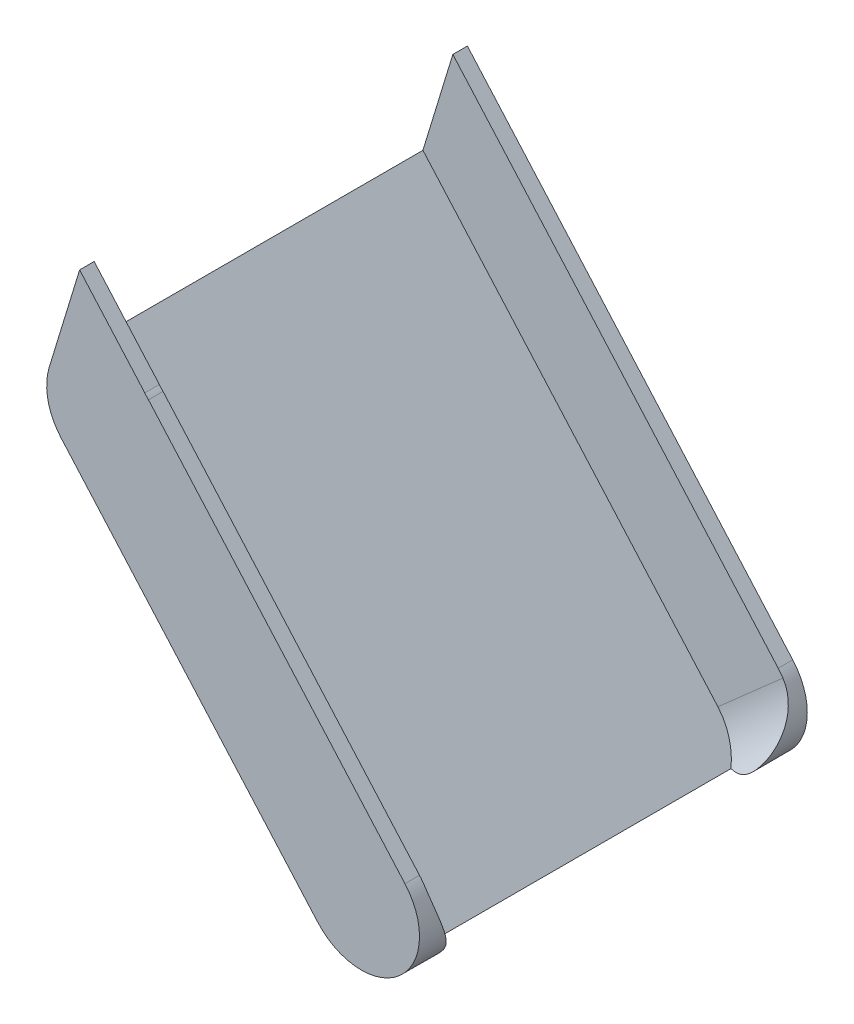
SolidWorks part; units mm, degrees
material "EPDM"
ref_plane "Front Plane" through (0, 0, 0) normal (0, 0, 1) x (1, 0, 0)
ref_plane "Top Plane" through (0, 0, 0) normal (0, 1, 0) x (1, 0, 0)
ref_plane "Right Plane" through (0, 0, 0) normal (1, 0, 0) x (0, 0, -1)
sketch "Sketch1" plane through (0, 0, 0) normal (0, 0, 1) x (1, 0, 0)
  line L0 (0, 0) -> (132.2876, -150) construction
  line L1 (22.5, 19.8431) -> (154.7876, -130.1569)
  line L2 (-22.5, -19.8431) -> (109.7876, -169.8431)
  arc A0 (22.5, 19.8431) -> (-22.5, -19.8431) centre (0, 0) ccw
  arc A1 (109.7876, -169.8431) -> (154.7876, -130.1569) centre (132.2876, -150) ccw
  point P3 (66.1438, -75)
  dimension "D1" = 30
  dimension "D2" = 150
  dimension "D3" = 200
extrude "Boss-Extrude4" add sketch "Sketch1" along normal blind 200
sketch "Sketch4" plane through (22.5, 19.8431, 0) normal (0.75, 0.6614, 0) x (0, 0, -1)
  line L2 (-192.5, 51.3214) -> (-192.5, -204.0082)
  line L4 (-7.5, 51.3214) -> (-7.5, -204.0082)
  line L6 (-200, -200) -> (-200, 0) construction
  line L7 (-192.5, 51.3214) -> (-7.5, 51.3214)
  line L8 (-157.5, -239.0082) -> (-42.5, -239.0082)
  arc A0 (-42.5, -239.0082) -> (-7.5, -204.0082) centre (-42.5, -204.0082) ccw
  arc A1 (-157.5, -239.0082) -> (-192.5, -204.0082) centre (-157.5, -204.0082) cw
  dimension "D1" = 35
  dimension "D3" = 185
  dimension "D4" = 7.5
extrude "Cut-Extrude5" cut sketch "Sketch4" against normal blind 45
sketch "Sketch5" plane through (0, 0, 0) normal (0, 0, -1) x (-1, 0, 0)
  line L0 (28.6922, 8.7612) -> (-20.5985, 170.1849)
  line L1 (-22.5, 19.8431) -> (13.0126, 60.1107)
  line L2 (-22.5, 19.8431) -> (28.6922, 8.7612)
  arc A0 (22.5, -19.8431) -> (-22.5, 19.8431) centre (0, 0) ccw construction
  arc M1 (22.5, -19.8431) -> (-22.5, 19.8431) centre (0, 0) ccw
extrude "Boss-Extrude5" add sketch "Sketch5" against normal blind 7.5 contours L1 L0 M1
sketch "Sketch6" plane through (0, 0, 192.5) normal (0, 0, -1) x (-1, 0, 0)
  line L0 (-20.6319, 21.9613) -> (13.0126, 60.1107)
  line L1 (-154.7876, -130.1569) -> (13.0126, 60.1107) construction
  line L2 (13.0126, 60.1107) -> (28.6922, 8.7612)
  line L3 (28.6922, 8.7612) -> (-20.6319, 21.9613)
extrude "Boss-Extrude6" add sketch "Sketch6" against normal blind 7.5
